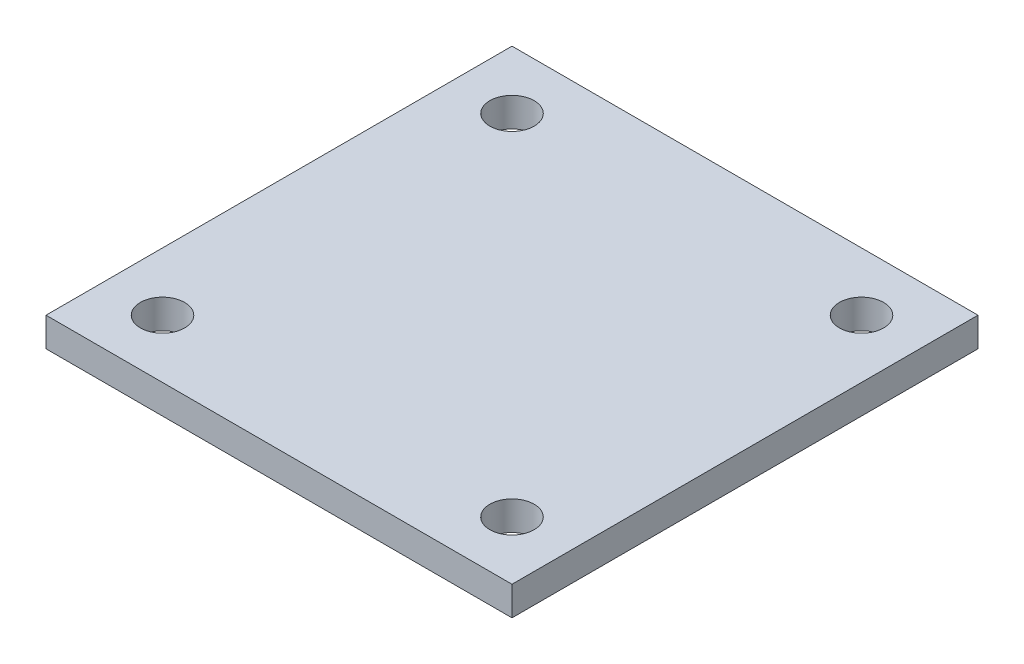
SolidWorks part; units mm, degrees
ref_plane "Front Plane" through (0, 0, 0) normal (0, 0, 1) x (1, 0, 0)
ref_plane "Top Plane" through (0, 0, 0) normal (0, 1, 0) x (1, 0, 0)
ref_plane "Right Plane" through (0, 0, 0) normal (1, 0, 0) x (0, 0, -1)
sketch "Sketch1" plane through (0, 0, 0) normal (0, 1, 0) x (1, 0, 0)
  line L1 (50.8, 50.8) -> (-50.8, 50.8)
  line L2 (50.8, 50.8) -> (50.8, -50.8)
  line L3 (50.8, -50.8) -> (-50.8, -50.8)
  line L4 (-50.8, 50.8) -> (-50.8, -50.8)
  line L5 (50.8, 50.8) -> (-50.8, -50.8) construction
  line L6 (50.8, -50.8) -> (-50.8, 50.8) construction
  point P0 (0, 0)
  dimension "D1" = 101.6
  dimension "D2" = 101.6
extrude "Boss-Extrude1" add sketch "Sketch1" along normal blind 6.35
sketch "Sketch2" plane through (0, 6.35, 0) normal (0, 1, 0) x (1, 0, 0)
  line L0 (-50.8, -50.8) -> (50.8, -50.8) construction
  line L1 (-50.8, 50.8) -> (-50.8, -50.8) construction
  line L2 (50.8, -50.8) -> (50.8, 50.8) construction
  line L3 (50.8, 50.8) -> (-50.8, 50.8) construction
  circle A0 centre (-38.1, 38.1) radius 4.826
  circle A1 centre (38.1, 38.1) radius 4.826
  circle A2 centre (38.1, -38.1) radius 4.826
  circle A3 centre (-38.1, -38.1) radius 4.826
  point P14 (0, 0)
  point P15 (0, 0)
  point P18 (0, 0)
  point P19 (0, 0)
  dimension "D3" = 9.652
  dimension "D4" = 9.652
  dimension "D7" = 9.652
  dimension "D8" = 9.652
  dimension "D1" = 12.7
  dimension "D2" = 12.7
  dimension "D5" = 12.7
  dimension "D6" = 12.7
extrude "Cut-Extrude1" cut sketch "Sketch2" against normal blind 6.35
